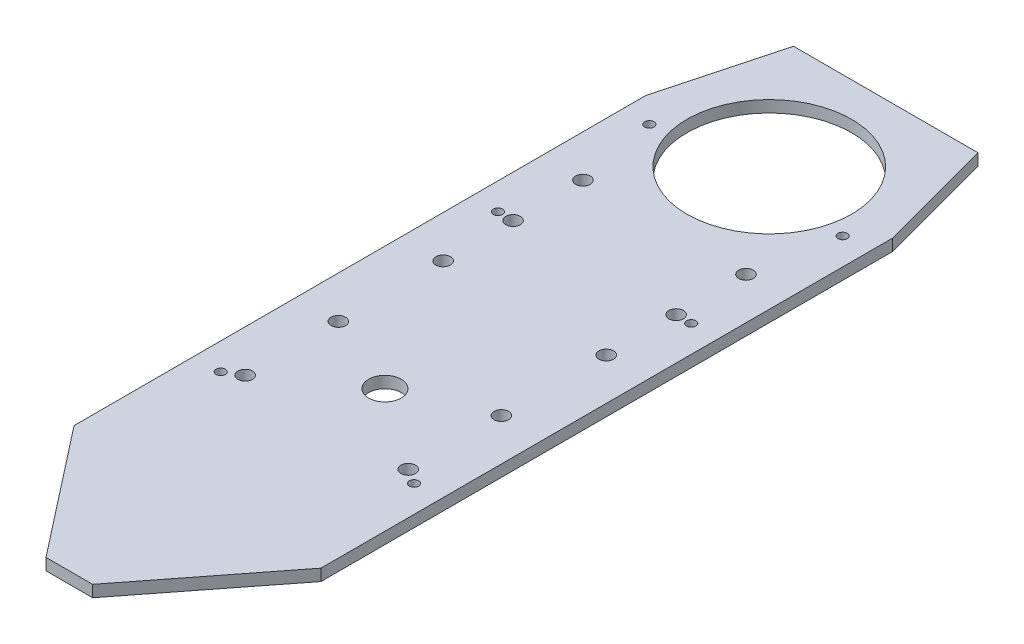
SolidWorks part; units mm, degrees
material "AISI 1045 Steel, cold drawn"
ref_plane "Front Plane" through (0, 0, 0) normal (0, 0, 1) x (1, 0, 0)
ref_plane "Top Plane" through (0, 0, 0) normal (0, 1, 0) x (1, 0, 0)
ref_plane "Right Plane" through (0, 0, 0) normal (1, 0, 0) x (0, 0, -1)
sketch "Sketch23" plane through (0, 0, 0) normal (0, 1, 0) x (1, 0, 0)
  line L0 (0, 0) -> (0, -601) construction
  line L6 (70, -260) -> (70, -400) construction
  line L10 (106, -490.925) -> (106, 0)
  line L12 (-106, -490.925) -> (-106, 0)
  line L14 (-106, 0) -> (-79.2051, 100)
  line L15 (79.2051, 100) -> (-79.2051, 100)
  line L16 (106, 0) -> (79.2051, 100)
  line L17 (-20, -601) -> (20, -601)
  line L18 (20, -601) -> (106, -490.925)
  line L19 (-20, -601) -> (-106, -490.925)
  circle A0 centre (0, 0) radius 70.65
  circle A2 centre (0, -330) radius 14
  point P15 (0, -601)
  point P25 (0, -601)
  point P26 (0, 100)
  dimension "D1" = 141.3
  dimension "D3" = 28
  dimension "D4" = 330
  dimension "D13" = 40
  dimension "D14" = 128
  dimension "D2" = 601
  dimension "D6" = 140
  dimension "D10" = 105
  dimension "D11" = 100
  dimension "D15" = 212
  dimension "D16" = 158.4102
extrude "Boss-Extrude3" add sketch "Sketch23" along normal blind 10
sketch "Sketch24" plane through (0, 10, 0) normal (0, 1, 0) x (1, 0, 0)
  line L0 (0, 0) -> (0, -520.2754) construction
  line L1 (-70, -380) -> (-70, 100) construction
  line L20 (79.2051, 100) -> (-79.2051, 100) construction
  circle A0 centre (-83, -150) radius 4
  circle A1 centre (-83, -388) radius 4
  circle A2 centre (83, -388) radius 4
  circle A3 centre (83, -150) radius 4
  circle A4 centre (-83, -20) radius 4
  circle A5 centre (83, -20) radius 4
  circle A7 centre (-70, -380) radius 6.25
  circle A8 centre (-70, -300) radius 6.25
  circle A9 centre (-70, -210) radius 6.25
  circle A10 centre (-70, -150) radius 6.25
  circle A11 centre (-70, -90) radius 6.25
  circle A12 centre (70, -90) radius 6.25
  circle A13 centre (70, -150) radius 6.25
  circle A14 centre (70, -210) radius 6.25
  circle A15 centre (70, -300) radius 6.25
  circle A16 centre (70, -380) radius 6.25
  circle A17 centre (0, -330) radius 14 construction
  dimension "D1" = 8
  dimension "D3" = 238
  dimension "D4" = 83
  dimension "D5" = 130
  dimension "D6" = 12.5
  dimension "D7" = 13
  dimension "D8" = 8
  dimension "D9" = 80
  dimension "D10" = 60
  dimension "D11" = 60
  dimension "D12" = 90
  dimension "D13" = 50
  dimension "D14" = 70
  dimension "D2" = 150
extrude "lo bat hop so" cut sketch "Sketch24" against normal up to next
sketch "Bend-Lines1" [suppressed] plane through (0, 0, 0) normal (0, 1, 0) x (1, 0, 0)
sketch "Bounding-Box1" [suppressed] plane through (0, 0, 0) normal (0, 1, 0) x (1, 0, 0)
